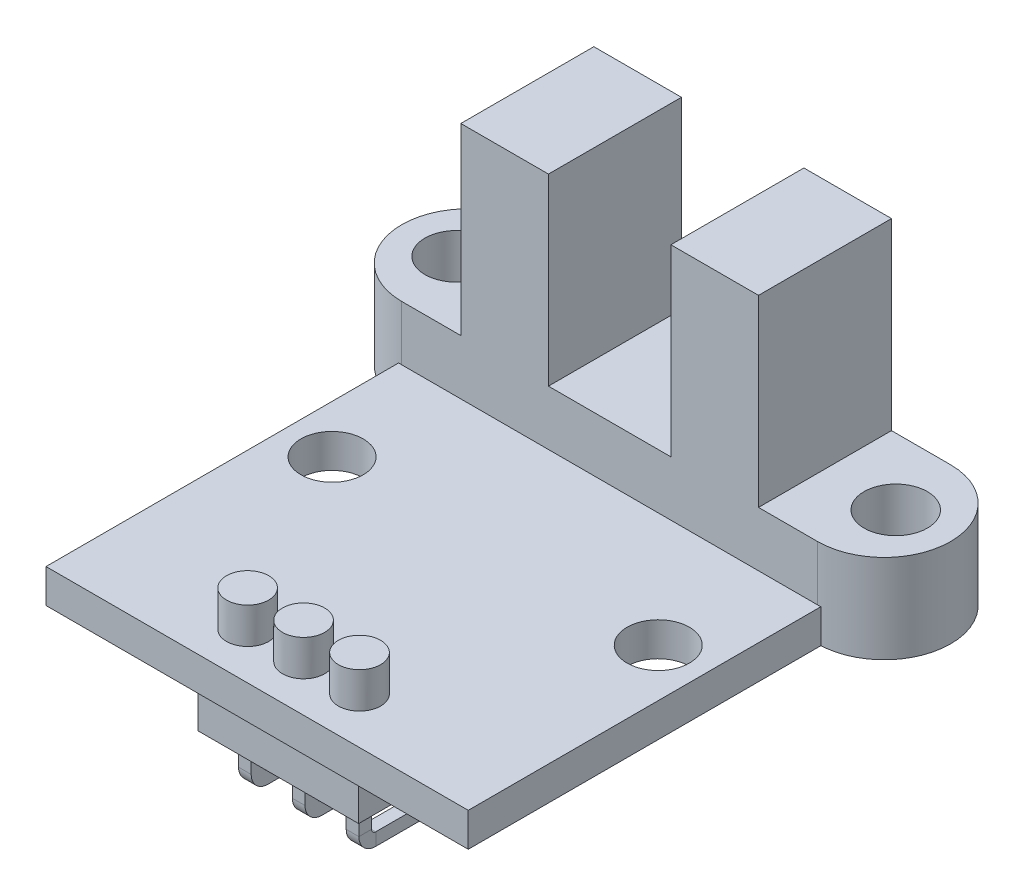
SolidWorks part; units mm, degrees
ref_plane "Front Plane" through (0, 0, 0) normal (0, 0, 1) x (1, 0, 0)
ref_plane "Top Plane" through (0, 0, 0) normal (0, 1, 0) x (1, 0, 0)
ref_plane "Right Plane" through (0, 0, 0) normal (1, 0, 0) x (0, 0, -1)
sketch "Sketch1" plane through (0, 0, 0) normal (0, 1, 0) x (1, 0, 0)
  line L0 (-9.85, 0) -> (9.85, 0) construction
  line L1 (-9.85, 3.15) -> (9.85, 3.15)
  line L2 (-9.85, -3.15) -> (9.85, -3.15)
  line L3 (-13, 0) -> (-11.9, 0) construction
  line L4 (11.9, 0) -> (13, 0) construction
  arc A0 (-9.85, 3.15) -> (-9.85, -3.15) centre (-9.85, 0) ccw
  arc A1 (9.85, -3.15) -> (9.85, 3.15) centre (9.85, 0) ccw
  circle A2 centre (-10.4, 0) radius 1.5
  circle A3 centre (10.4, 0) radius 1.5
  point P2 (0, 0)
  dimension "D1" = 26
  dimension "D3" = 3
  dimension "D4" = 17.8
  dimension "D2" = 6.3
extrude "Boss-Extrude1" add sketch "Sketch1" along normal blind 2.6
sketch "Sketch2" plane through (0, 2.6, 0) normal (0, 1, 0) x (1, 0, 0)
  line L0 (9.85, 3.15) -> (-9.85, 3.15) construction
  line L1 (-7.05, -3.15) -> (7.05, -3.15)
  line L2 (-7.05, -3.15) -> (-7.05, 3.15)
  line L3 (-7.05, 3.15) -> (7.05, 3.15)
  line L4 (7.05, -3.15) -> (7.05, 3.15)
  line L5 (-7.05, -3.15) -> (7.05, 3.15) construction
  line L6 (-7.05, 3.15) -> (7.05, -3.15) construction
  line L8 (2.9, -3.15) -> (-2.9, -3.15)
  line L9 (2.9, -3.15) -> (2.9, 3.15)
  line L10 (2.9, 3.15) -> (-2.9, 3.15)
  line L11 (-2.9, -3.15) -> (-2.9, 3.15)
  line L12 (2.9, -3.15) -> (-2.9, 3.15) construction
  line L13 (2.9, 3.15) -> (-2.9, -3.15) construction
  point P0 (0, 0)
  point P8 (0, 0)
  line M7 (-9.85, -3.15) -> (9.85, -3.15)
  line M9 (9.85, 3.15) -> (-9.85, 3.15)
  dimension "D1" = 14.1
  dimension "D2" = 5.8
extrude "Boss-Extrude2" add sketch "Sketch2" along normal blind 8.7 contours L11 L2 M7 M9 | L9 L4 M7 M9
sketch "Sketch3" plane through (0, 0, 0) normal (0, -1, 0) x (1, 0, 0)
  line L0 (0, 0) -> (0, 15.1335) construction
  line L2 (-9.85, -3.15) -> (9.85, -3.15)
  line L3 (9.85, 3.15) -> (-9.85, 3.15)
  line L4 (-9.85, -3.15) -> (9.85, -3.15)
  line L5 (9.85, 3.15) -> (-9.85, 3.15)
  line L6 (-10, 19.85) -> (10, 19.85)
  line L7 (-10, 19.85) -> (-10, 3.15)
  line L8 (-10, 3.15) -> (10, 3.15)
  line L9 (10, 19.85) -> (10, 3.15)
  line L10 (-10, 19.85) -> (10, 3.15) construction
  line L11 (-10, 3.15) -> (10, 19.85) construction
  line L12 (-10, 3.15) -> (10, 3.15)
  line L13 (-10, 3.15) -> (-10, 2.1759)
  line L14 (-10, 2.1759) -> (10, 2.1759)
  line L15 (10, 3.15) -> (10, 2.1759)
  arc A3 (-9.85, 3.15) -> (-9.85, -3.15) centre (-9.85, 0) ccw
  arc A4 (9.85, -3.15) -> (9.85, 3.15) centre (9.85, 0) ccw
  arc A5 (-9.85, 3.15) -> (-9.85, -3.15) centre (-9.85, 0) ccw
  arc A6 (9.85, -3.15) -> (9.85, 3.15) centre (9.85, 0) ccw
  point P2 (0, 11.5)
  arc M9 (-9.85, 3.15) -> (-9.85, -3.15) centre (-9.85, 0) ccw
  line M10 (-9.85, -3.15) -> (9.85, -3.15)
  arc M11 (9.85, -3.15) -> (9.85, 3.15) centre (9.85, 0) ccw
  line M12 (9.85, 3.15) -> (-9.85, 3.15)
  circle M13 centre (-10.4, 0) radius 1.5
  circle M14 centre (10.4, 0) radius 1.5
  dimension "D2" = 23
  dimension "D3" = 20
  dimension "D1" = 0
extrude "Boss-Extrude3" add sketch "Sketch3" along normal blind 1.6 contours L9 L6 L7 L8 M12 | L15 L13 L14 M11 M12 M9 | L15 L14 L13 M11 M9 M10 M13 M14
sketch "Sketch4" plane through (0, 0, 0) normal (0, 1, 0) x (1, 0, 0)
  line L0 (-10, -17.65) -> (10, -17.65) construction
  line L1 (-10, -19.85) -> (-10, -3.15) construction
  line L2 (10, -19.85) -> (10, -3.15) construction
  line L5 (0, -17.65) -> (0, -14.4826) construction
  line L6 (0, -14.4826) -> (-2.65, -17.65) construction
  line L7 (0, -14.4826) -> (2.65, -17.65) construction
  line L8 (-10, -19.85) -> (10, -19.85) construction
  circle A0 centre (0, -17.65) radius 1
  circle A1 centre (2.65, -17.65) radius 1
  circle A2 centre (-2.65, -17.65) radius 1
  dimension "D1" = 2
  dimension "D2" = 7.3
  dimension "D3" = 3.2
extrude "Boss-Extrude4" add sketch "Sketch4" along normal blind 1.7
sketch "Sketch5" plane through (0, 0, 0) normal (0, 1, 0) x (1, 0, 0)
  line L0 (-10, -8.575) -> (10, -8.575) construction
  line L1 (-10, -19.85) -> (-10, -3.15) construction
  line L2 (10, -19.85) -> (10, -3.15) construction
  line L3 (-7.725, -8.575) -> (-10, -19.85) construction
  line L4 (10, -19.85) -> (7.725, -8.575) construction
  line L8 (-10, -19.85) -> (10, -19.85) construction
  circle A0 centre (-7.725, -8.575) radius 1.475
  circle A1 centre (7.725, -8.575) radius 1.475
  dimension "D1" = 0.8
  dimension "D2" = 2.95
  dimension "D3" = 9.8
extrude "Cut-Extrude1" cut sketch "Sketch5" against normal through all
sketch "Sketch6" plane through (0, -1.6, 0) normal (0, -1, 0) x (1, 0, 0)
  line L0 (0, 0) -> (0, 19.85) construction
  line L1 (-10, 19.85) -> (10, 19.85) construction
  line L2 (-9.85, -3.15) -> (9.85, -3.15) construction
  line L3 (-2.15, 3.55) -> (2.15, 3.55)
  line L4 (-2.15, 3.55) -> (-2.15, 8.55)
  line L5 (-2.15, 8.55) -> (2.15, 8.55)
  line L6 (2.15, 3.55) -> (2.15, 8.55)
  line L7 (-2.15, 3.55) -> (2.15, 8.55) construction
  line L8 (-2.15, 8.55) -> (2.15, 3.55) construction
  point P5 (0, 6.05)
  dimension "D1" = 4.3
  dimension "D2" = 5
  dimension "D3" = 6.7
extrude "Boss-Extrude5" add sketch "Sketch6" along normal blind 2
sketch "Sketch7" plane through (0, -1.6, 0) normal (0, -1, 0) x (1, 0, 0)
  line L0 (0, 19.85) -> (0, 8.55) construction
  line L1 (-10, 19.85) -> (10, 19.85) construction
  line L2 (2.15, 8.55) -> (-2.15, 8.55) construction
  line L4 (-3.81, 16.31) -> (3.81, 16.31)
  line L5 (-3.81, 16.31) -> (-3.81, 18.85)
  line L6 (-3.81, 18.85) -> (3.81, 18.85)
  line L7 (3.81, 16.31) -> (3.81, 18.85)
  line L8 (-3.81, 16.31) -> (3.81, 18.85) construction
  line L9 (-3.81, 18.85) -> (3.81, 16.31) construction
  point P6 (0, 17.58)
  dimension "D1" = 7.62
  dimension "D2" = 2.54
  dimension "D3" = 1
extrude "Boss-Extrude6" add sketch "Sketch7" along normal blind 2.54
sketch "Sketch8" plane through (0, 0, 0) normal (1, 0, 0) x (0, 0, -1)
  line L0 (-17.58, -4.14) -> (-17.58, -5.64)
  line L1 (-16.31, -4.14) -> (-18.85, -4.14) construction
  line L2 (-17.08, -6.14) -> (-10.88, -6.14)
  arc A0 (-17.58, -5.64) -> (-17.08, -6.14) centre (-17.08, -5.64) ccw
  dimension "D1" = 6.7
  dimension "D3" = 0.5
  dimension "D2" = 2
sketch "Sketch9" plane through (0, -4.14, 0) normal (0, -1, 0) x (1, 0, 0)
  line L0 (0, 17.08) -> (0, 17.58) construction
  line L1 (-2.85, 17.28) -> (2.85, 17.28)
  line L2 (-2.85, 17.28) -> (-2.85, 17.88)
  line L3 (-2.85, 17.88) -> (2.85, 17.88)
  line L4 (2.85, 17.28) -> (2.85, 17.88)
  line L5 (-2.85, 17.28) -> (2.85, 17.88) construction
  line L6 (-2.85, 17.88) -> (2.85, 17.28) construction
  line L7 (-3.81, 17.58) -> (3.81, 17.58) construction
  line L8 (-3.81, 18.85) -> (-3.81, 16.31) construction
  line L9 (3.81, 16.31) -> (3.81, 18.85) construction
  line L10 (0, 18.85) -> (0, 17.58) construction
  line L11 (3.81, 18.85) -> (-3.81, 18.85) construction
  point P0 (0, 17.58)
  dimension "D1" = 0.6
  dimension "D2" = 5.7
sweep "Sweep1" add profiles "Sketch9" path "Sketch8"
sketch "Sketch10" plane through (0, -6.44, 0) normal (0, -1, 0) x (1, 0, 0)
  line L0 (-2.85, 10.88) -> (-2.25, 10.88) construction
  line L1 (2.85, 10.88) -> (-2.85, 10.88) construction
  line L2 (-2.25, 10.88) -> (-0.3, 10.88) construction
  line L3 (-0.3, 10.88) -> (0.3, 10.88) construction
  line L4 (0.3, 10.88) -> (2.25, 10.88) construction
  line L5 (2.25, 10.88) -> (2.85, 10.88) construction
  line L6 (-2.25, 10.88) -> (-2.25, 17.88)
  line L7 (2.85, 17.88) -> (-2.85, 17.88) construction
  line L8 (-2.25, 17.88) -> (-0.3, 17.88)
  line L9 (-0.3, 17.88) -> (-0.3, 10.88)
  line L10 (-0.3, 10.88) -> (-2.25, 10.88)
  line L11 (0.3, 10.88) -> (2.25, 10.88)
  line L12 (2.25, 10.88) -> (2.25, 17.88)
  line L13 (2.25, 17.88) -> (0.3, 17.88)
  line L14 (0.3, 17.88) -> (0.3, 10.88)
  dimension "D1" = 0.6
extrude "Cut-Extrude2" cut sketch "Sketch10" against normal up to surface (2.3 mm away) up to face at (0, -4.14, 17.58)
sketch "Sketch11" plane through (0, 11.3, 0) normal (0, 1, 0) x (1, 0, 0)
  line L0 (-7.05, 0) -> (7.05, 0) construction
  line L1 (-7.05, -3.15) -> (-7.05, 3.15) construction
  line L2 (7.05, -3.15) -> (7.05, 3.15) construction
